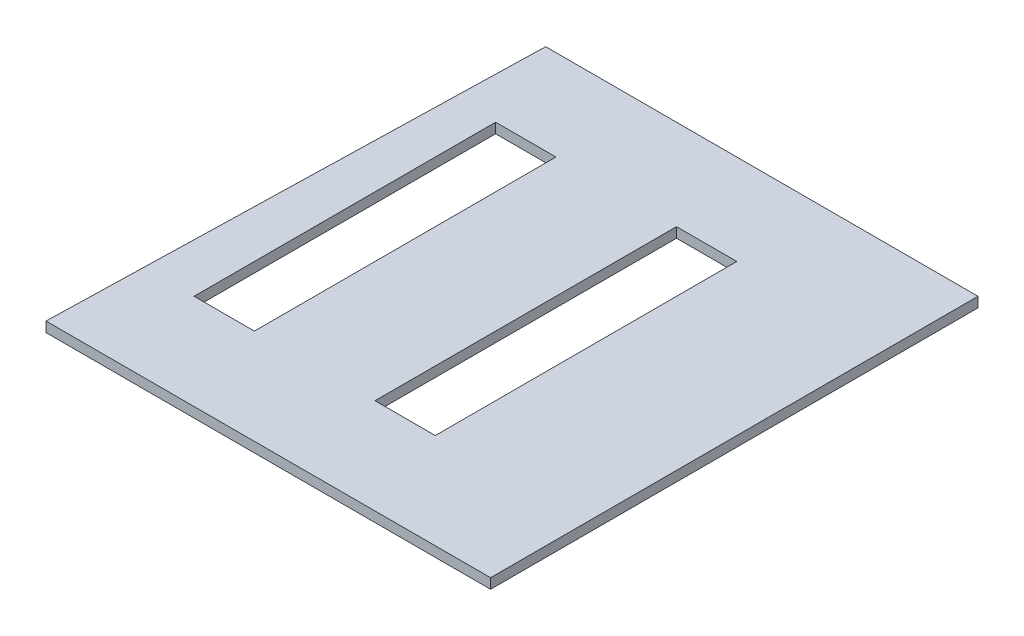
SolidWorks part; units mm, degrees
material "Polyurethane Foam Flexible"
ref_plane "Front Plane" through (0, 0, 0) normal (0, 0, 1) x (1, 0, 0)
ref_plane "Top Plane" through (0, 0, 0) normal (0, 1, 0) x (1, 0, 0)
ref_plane "Right Plane" through (0, 0, 0) normal (1, 0, 0) x (0, 0, -1)
sketch "Sketch1" plane through (0, 0, 0) normal (0, 1, 0) x (1, 0, 0)
  line L0 (-1123.7134, -1232.0583) -> (-1061.7374, 1231.7417)
  line L1 (-1061.7374, 1231.7417) -> (1123.4246, 1231.7417)
  line L3 (-1123.7134, -1232.0583) -> (1123.4246, -1232.0583)
  line L4 (1123.4246, 1231.7417) -> (1123.4246, -1232.0583)
  line L5 (-1063.3858, 1166.2138) -> (1123.4246, -1232.0583) construction
  line L6 (-1123.7134, -1232.0583) -> (1123.4246, 1231.7417) construction
  point P0 (0, 0)
  dimension "D1" = 2247.138
  dimension "D2" = 2463.8
  dimension "D3" = 2185.162
  dimension "D4" = 65.5278
extrude "Boss-Extrude1" add sketch "Sketch1" along normal blind 50.8
sketch "Sketch2" plane through (0, 50.8, 0) normal (0, 1, 0) x (1, 0, 0)
  line L0 (1123.4246, 1231.7417) -> (-1061.7374, 1231.7417) construction
  line L1 (56.6246, -749.4583) -> (361.4246, -749.4583)
  line L2 (56.6246, -749.4583) -> (56.6246, 774.5417)
  line L3 (56.6246, 774.5417) -> (361.4246, 774.5417)
  line L4 (361.4246, -749.4583) -> (361.4246, 774.5417)
  line L5 (56.6246, -749.4583) -> (361.4246, 774.5417) construction
  line L6 (56.6246, 774.5417) -> (361.4246, -749.4583) construction
  line L7 (-857.7754, -749.4583) -> (-552.9754, -749.4583)
  line L8 (-857.7754, -749.4583) -> (-857.7754, 774.5417)
  line L9 (-857.7754, 774.5417) -> (-552.9754, 774.5417)
  line L10 (-552.9754, -749.4583) -> (-552.9754, 774.5417)
  line L11 (-857.7754, -749.4583) -> (-552.9754, 774.5417) construction
  line L12 (-857.7754, 774.5417) -> (-552.9754, -749.4583) construction
  line L13 (1123.4246, -1232.0583) -> (1123.4246, 1231.7417) construction
  point P0 (209.0246, 12.5417)
  point P5 (-705.3754, 12.5417)
  dimension "D1" = 457.2
  dimension "D2" = 304.8
  dimension "D3" = 609.6
  dimension "D4" = 304.8
  dimension "D5" = 762
  dimension "D6" = 1524
extrude "Cut-Extrude1" cut sketch "Sketch2" against normal up to surface (50.8 mm away) up to face at (15.3496, 0, 0.1583)
